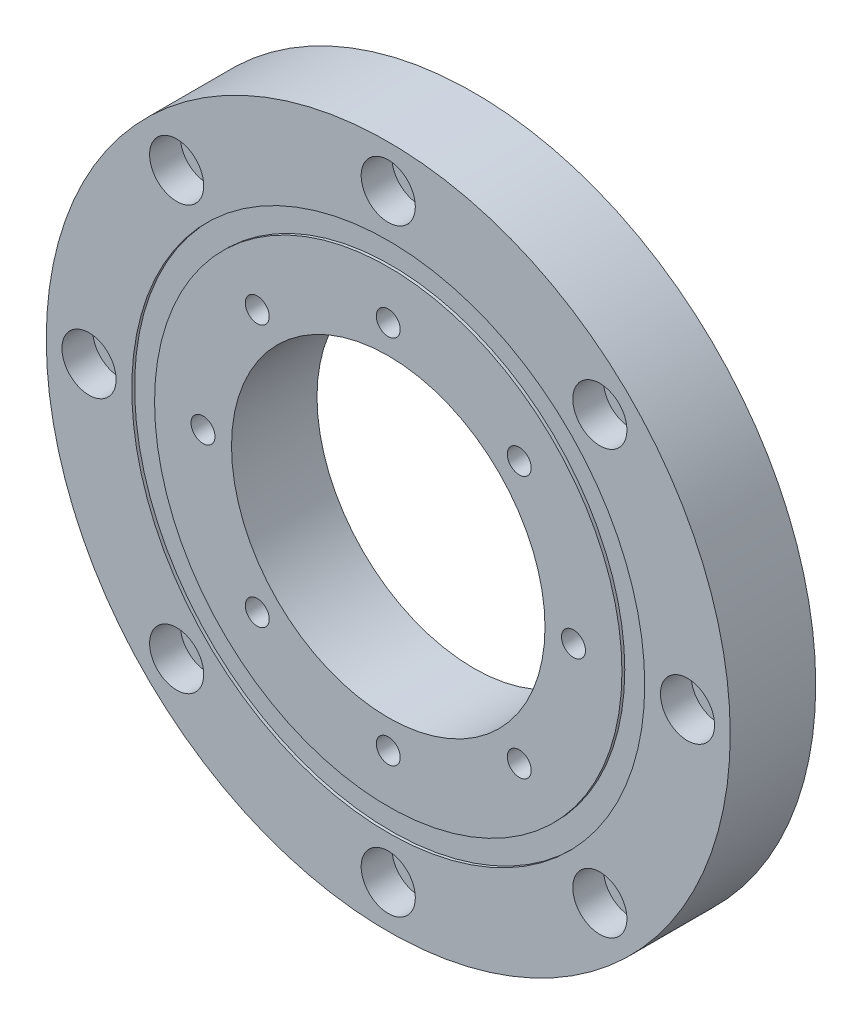
SolidWorks part; units mm, degrees
material "AISI 304"
ref_plane "前基準面" through (0, 0, 0) normal (0, 0, 1) x (1, 0, 0)
ref_plane "上基準面" through (0, 0, 0) normal (0, 1, 0) x (1, 0, 0)
ref_plane "右基準面" through (0, 0, 0) normal (1, 0, 0) x (0, 0, -1)
sketch "草圖1" plane through (0, 0, 0) normal (0, 0, 1) x (1, 0, 0)
  circle A0 centre (0, 0) radius 60
  dimension "D1" = 120
extrude "填料-伸長1" add sketch "草圖1" along normal mid plane 15
sketch "草圖2" plane through (0, 0, 7.5) normal (0, 0, 1) x (1, 0, 0)
  circle A0 centre (0, 0) radius 27.5
  dimension "D1" = 55
extrude "除料-伸長1" cut sketch "草圖2" against normal through all
sketch "草圖3" plane through (0, 0, 7.5) normal (0, 0, 1) x (1, 0, 0)
  circle A0 centre (0, 0) radius 41
  circle A1 centre (0, 0) radius 45
  dimension "D1" = 90
  dimension "D2" = 82
extrude "除料-伸長2" cut sketch "草圖3" against normal blind 0.5
mirror "鏡射1" about plane through (0, 0, 0) normal (0, 0, 1) of "除料-伸長2"
hole_wizard "M5 凹頭蓋螺釘的柱孔1" positions "草圖4" profile "草圖5" counterbore size "M5" standard "Ansi Metric" end condition through all
sketch "草圖4" plane through (0, 0, 7.5) normal (0, 0, 1) x (1, 0, 0)
  line L3 (0, 52.5) -> (0, -52.5) construction
  point P7 (0, 52.5)
  dimension "D1" = 105
sketch "草圖5" plane through (0, 52.5, 7.5) normal (1, 0, 0) x (0, -1, 0)
  line L0 (0, 0) -> (0, 15)
  line L1 (0, 15) -> (2.75, 15)
  line L3 (2.75, 15) -> (2.75, 5.4)
  line L4 (2.75, 5.4) -> (4.75, 5.4)
  line L5 (4.75, 5.4) -> (4.75, 0)
  line L7 (4.75, 0) -> (0, 0)
  line L11 (0, -6.35) -> (0, 107.95) construction
  dimension "貫穿孔直徑" = 5.5
  dimension "貫穿孔深度" = 15
  dimension "柱孔直徑" = 9.5
  dimension "柱孔深度" = 5.4
hole_wizard "M5x0.8 螺紋孔1" positions "草圖6" profile "草圖8" tap size "M5x0.8" standard "Ansi Metric" end condition through all
sketch "草圖6" plane through (0, 0, 7.5) normal (0, 0, 1) x (1, 0, 0)
  line L0 (0, -32.5) -> (0, 32.5) construction
  point P1 (0, 32.5)
  dimension "D1" = 65
sketch "草圖8" plane through (0, 32.5, 7.5) normal (1, 0, 0) x (0, -1, 0)
  line L0 (0, 0) -> (0, 15)
  line L1 (0, 15) -> (2.1, 15)
  line L2 (2.1, 15) -> (2.1, 0)
  line L5 (2.1, 0) -> (0, 0)
  line L11 (0, -6.35) -> (0, 107.95) construction
  dimension "貫穿螺孔鑽直徑" = 4.2
  dimension "貫穿螺孔鑽深度" = 15
pattern_circular "環狀複製排列1" count 8 over 360 about axis through (0, 0, 0) along (0, 0, 1) of "M5 凹頭蓋螺釘的柱孔1", "M5x0.8 螺紋孔1"
